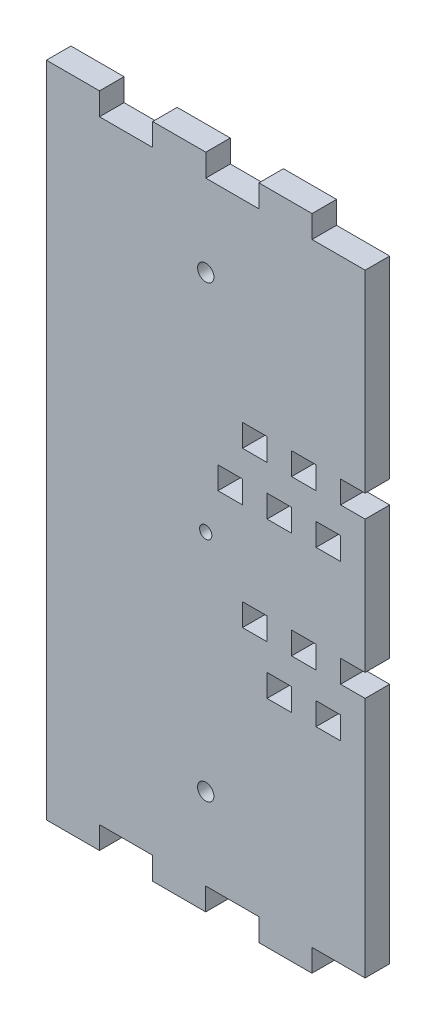
SolidWorks part; units mm, degrees
ref_plane "Front Plane" through (0, 0, 0) normal (0, 0, 1) x (1, 0, 0)
ref_plane "Top Plane" through (0, 0, 0) normal (0, 1, 0) x (1, 0, 0)
ref_plane "Right Plane" through (0, 0, 0) normal (1, 0, 0) x (0, 0, -1)
sketch "Model" plane through (0, 0, 0) normal (0, 0, 1) x (1, 0, 0)
  line L0 (136.5035, 63.2531) -> (136.503, 57.7544)
  line L1 (123.5035, 63.2557) -> (123.5043, 57.7525)
  line L2 (110.5049, 63.2584) -> (110.5043, 57.7506)
  line L3 (97.5049, 63.2597) -> (97.5057, 57.761)
  line L4 (84.5063, 63.2623) -> (84.5057, 57.7623)
  line L5 (71.5071, 57.7649) -> (71.5082, 63.2597)
  line L6 (136.503, 57.7544) -> (123.5043, 57.7525)
  line L7 (110.5043, 57.7506) -> (97.5057, 57.761)
  line L8 (84.5057, 57.7623) -> (71.5071, 57.7649)
  line L9 (149.5022, 63.2518) -> (136.5035, 63.2531)
  line L10 (123.5035, 63.2557) -> (110.5049, 63.2584)
  line L11 (97.5049, 63.2597) -> (84.5063, 63.2623)
  line L12 (84.5213, 213.2544) -> (97.52, 213.2544)
  line L13 (110.52, 213.2531) -> (123.5186, 213.2531)
  line L14 (136.5186, 213.2531) -> (149.5172, 213.2518)
  line L15 (136.5186, 213.2531) -> (136.5191, 218.7518)
  line L16 (123.5186, 213.2531) -> (123.5205, 218.7563)
  line L17 (110.52, 213.2531) -> (110.5205, 218.7609)
  line L18 (97.52, 213.2544) -> (97.5219, 218.7531)
  line L19 (84.5213, 213.2544) -> (84.5219, 218.7544)
  line L20 (136.5191, 218.7518) -> (123.5205, 218.7563)
  line L21 (110.5205, 218.7609) -> (97.5219, 218.7531)
  line L22 (84.5219, 218.7544) -> (71.5232, 218.7544)
  line L26 (119.5122, 163.2548) -> (119.5125, 166.0048)
  line L27 (119.5125, 166.0048) -> (125.5125, 166.0042)
  line L28 (125.5125, 166.0042) -> (125.5119, 160.5042)
  line L29 (125.5119, 160.5042) -> (119.5119, 160.5048)
  line L30 (119.5119, 160.5048) -> (119.5122, 163.2548)
  line L31 (131.5122, 163.2536) -> (131.5125, 166.0036)
  line L32 (131.5125, 166.0036) -> (137.5125, 166.003)
  line L33 (137.5125, 166.003) -> (137.5119, 160.503)
  line L34 (137.5119, 160.503) -> (131.5119, 160.5036)
  line L35 (131.5119, 160.5036) -> (131.5122, 163.2536)
  line L36 (143.5122, 163.2524) -> (143.5125, 166.0024)
  line L37 (143.5125, 166.0024) -> (149.5125, 166.0018)
  line L38 (149.5119, 160.5018) -> (143.5119, 160.5024)
  line L39 (143.5119, 160.5024) -> (143.5122, 163.2524)
  line L40 (113.511, 151.2554) -> (113.5113, 154.0054)
  line L41 (113.5113, 154.0054) -> (119.5113, 154.0048)
  line L42 (119.5113, 154.0048) -> (119.5107, 148.5048)
  line L43 (119.5107, 148.5048) -> (113.5107, 148.5054)
  line L44 (113.5107, 148.5054) -> (113.511, 151.2554)
  line L45 (125.511, 151.2542) -> (125.5113, 154.0042)
  line L46 (125.5113, 154.0042) -> (131.5113, 154.0036)
  line L47 (131.5113, 154.0036) -> (131.5107, 148.5036)
  line L48 (131.5107, 148.5036) -> (125.5107, 148.5042)
  line L49 (125.5107, 148.5042) -> (125.511, 151.2542)
  line L50 (137.511, 151.253) -> (137.5113, 154.003)
  line L51 (137.5113, 154.003) -> (143.5113, 154.0024)
  line L52 (143.5107, 148.5024) -> (137.5107, 148.503)
  line L53 (137.5107, 148.503) -> (137.511, 151.253)
  line L54 (119.5084, 125.2548) -> (119.5087, 128.0048)
  line L55 (119.5087, 128.0048) -> (125.5087, 128.0042)
  line L56 (125.5087, 128.0042) -> (125.5081, 122.5042)
  line L57 (125.5081, 122.5042) -> (119.5081, 122.5048)
  line L58 (119.5081, 122.5048) -> (119.5084, 125.2548)
  line L59 (131.5084, 125.2536) -> (131.5087, 128.0036)
  line L60 (131.5087, 128.0036) -> (137.5087, 128.003)
  line L61 (137.5087, 128.003) -> (137.5081, 122.503)
  line L62 (137.5081, 122.503) -> (131.5081, 122.5036)
  line L63 (131.5081, 122.5036) -> (131.5084, 125.2536)
  line L64 (143.5084, 125.2524) -> (143.5087, 128.0024)
  line L65 (143.5087, 128.0024) -> (149.5087, 128.0018)
  line L66 (149.5022, 122.5018) -> (143.5081, 122.5024)
  line L67 (143.5081, 122.5024) -> (143.5084, 125.2524)
  line L68 (125.5072, 113.2542) -> (125.5075, 116.0042)
  line L69 (125.5075, 116.0042) -> (131.5075, 116.0036)
  line L70 (131.5075, 116.0036) -> (131.5069, 110.5036)
  line L71 (131.5069, 110.5036) -> (125.5069, 110.5042)
  line L72 (125.5069, 110.5042) -> (125.5072, 113.2542)
  line L73 (137.5072, 113.253) -> (137.5075, 116.003)
  line L74 (137.5075, 116.003) -> (143.5075, 116.0024)
  line L75 (143.5069, 110.5024) -> (137.5069, 110.503)
  line L76 (137.5069, 110.503) -> (137.5072, 113.253)
  line L77 (143.5113, 154.0024) -> (143.5107, 148.5024)
  line L78 (143.5075, 116.0024) -> (143.5069, 110.5024)
  line L79 (71.5232, 218.7544) -> (71.5082, 63.2597)
  line L80 (149.5125, 166.0018) -> (149.5172, 213.2518)
  line L81 (149.5119, 160.5018) -> (149.5087, 128.0018)
  line L82 (149.5022, 63.2518) -> (149.5022, 122.5018)
  circle A0 centre (110.5078, 83.257) radius 2
  circle A1 centre (110.5189, 193.2544) radius 2
  circle A2 centre (110.5073, 138.2557) radius 1.5
extrude "Boss-Extrude1" add sketch "Model" along normal blind 6 contours L30 L29 L28 L27 L26 | L35 L34 L33 L32 L31 | L49 L48 L47 L46 L45 | L44 L43 L42 L41 L40 | L77 L51 L50 L53 L52 | L63 L62 L61 L60 L59 | L72 L71 L70 L69 L68 | L78 L74 L73 L76 L75 | L79 L5 L8 L4 L11 L3 L7 L2 L10 L1 L6 L0 L9 L82 L66 L67 L64 L65 L81 L38 L39 L36 L37 L80 L14 L15 L20 L16 L13 L17 L21 L18 L12 L19 L22 | A1 | L57 L58 L54 L55 L56 | A0 | A2
